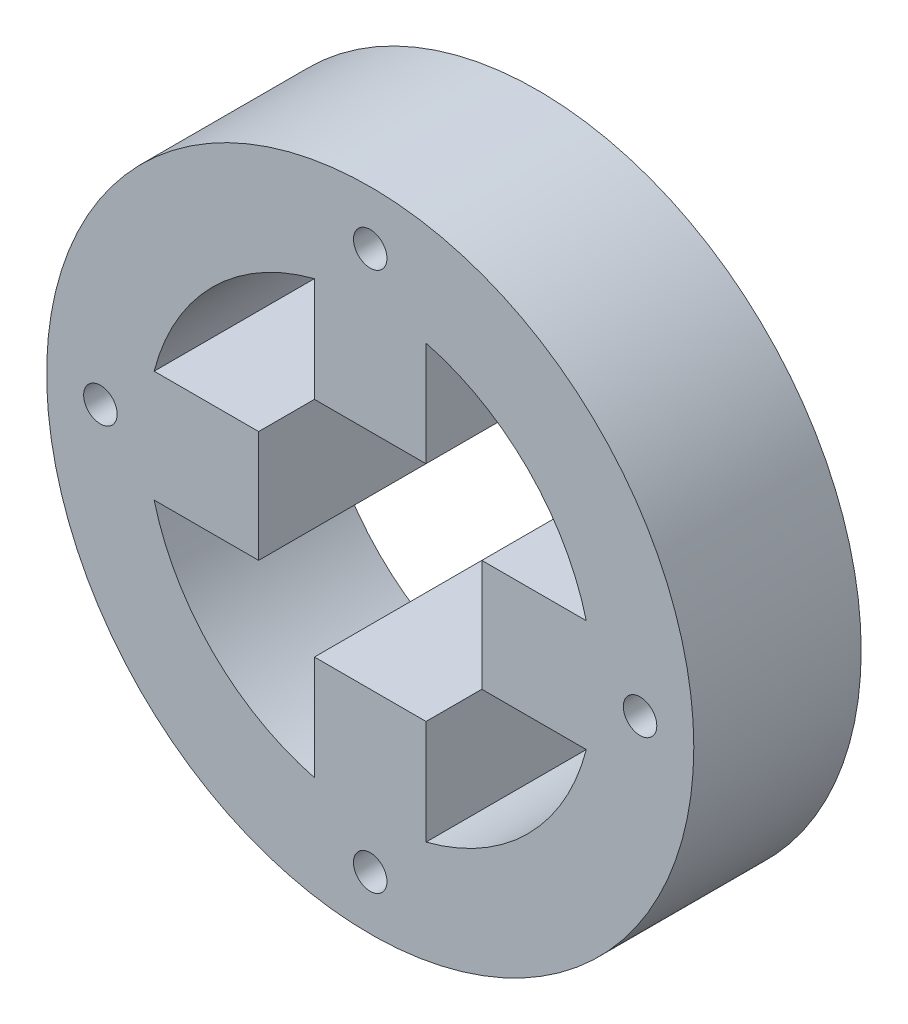
SolidWorks part; units mm, degrees
ref_plane "Front Plane" through (0, 0, 0) normal (0, 0, 1) x (1, 0, 0)
ref_plane "Top Plane" through (0, 0, 0) normal (0, 1, 0) x (1, 0, 0)
ref_plane "Right Plane" through (0, 0, 0) normal (1, 0, 0) x (0, 0, -1)
sketch "Sketch6" plane through (0, 0, 0) normal (0, 0, 1) x (1, 0, 0)
  circle A0 centre (0, 0) radius 20
  circle A1 centre (0, 0) radius 29
  dimension "D1" = 40
  dimension "D2" = 58
extrude "Inner Ring" add sketch "Sketch6" against normal blind 15 separate body
sketch "Sketch7" plane through (0, 0, 0) normal (0, 0, 1) x (1, 0, 0)
  line L2 (-10, 5) -> (-10, -5)
  line L3 (-5, 10) -> (5, 10)
  line L4 (10, 5) -> (10, -5)
  line L5 (-5, -10) -> (5, -10)
  line L14 (-19.3649, 5) -> (-10, 5)
  line L15 (-19.3649, -5) -> (-10, -5)
  line L16 (-5, 19.3649) -> (-5, 10)
  line L17 (5, 19.3649) -> (5, 10)
  line L18 (19.3649, 5) -> (10, 5)
  line L19 (19.3649, -5) -> (10, -5)
  line L20 (5, -19.3649) -> (5, -10)
  line L21 (-5, -19.3649) -> (-5, -10)
  circle A1 centre (0, 0) radius 20
  circle M19 centre (0, 0) radius 20
  dimension "D1" = 20
  dimension "D2" = 20
  dimension "D3" = 10
  dimension "D5" = 10
  dimension "D7" = 10
  dimension "D8" = 10
extrude "Motor Connector Cut" add sketch "Sketch7" against normal blind 15 contours L19 L18 L4 M19 | L17 L16 L3 M19 | L15 L2 L14 M19 | L21 L20 L5 M19
sketch "Sketch8" plane through (0, 0, 0) normal (0, 0, 1) x (1, 0, 0)
  circle A1 centre (0, 24.1825) radius 1.5
  circle A2 centre (24.1825, 0) radius 1.5
  circle A3 centre (0, -24.1825) radius 1.5
  circle A4 centre (-24.1825, 0) radius 1.5
  dimension "D1" = 3
  dimension "D2" = 3
  dimension "D3" = 3
  dimension "D4" = 3
  dimension "D6" = 48.3649
  dimension "D8" = 48.3649
extrude "M3 Holes" cut sketch "Sketch8" against normal blind 53 and the other way blind 38
